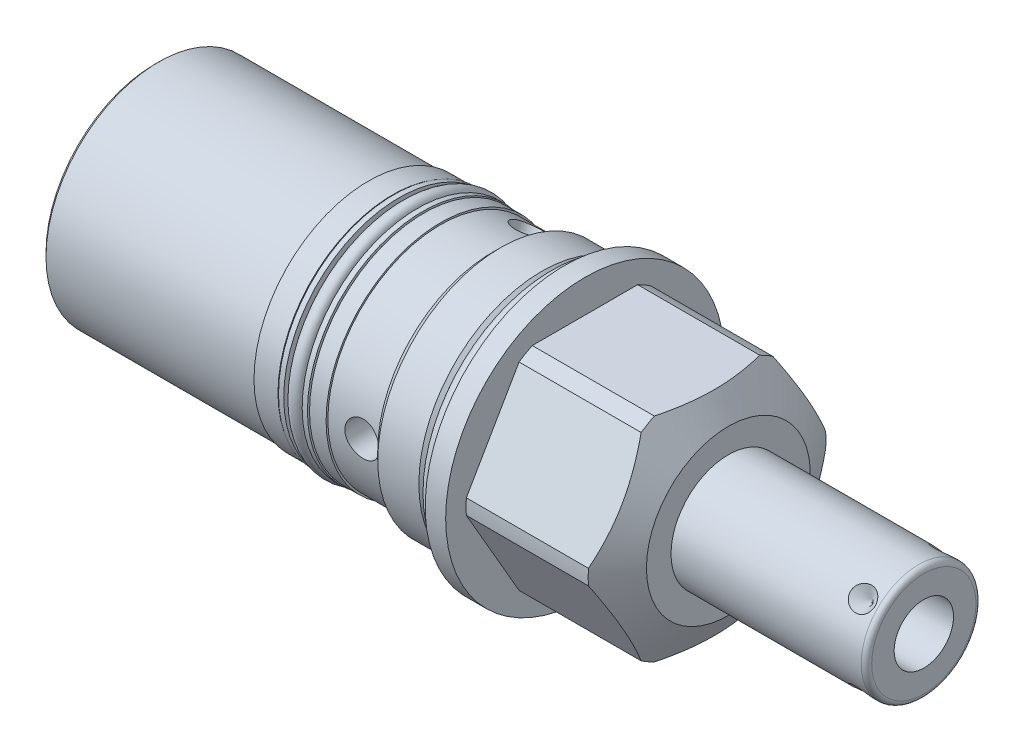
SolidWorks part; units mm, degrees
material "Alloy Steel"
ref_plane "Front Plane" through (0, 0, 0) normal (0, 0, 1) x (1, 0, 0)
ref_plane "Top Plane" through (0, 0, 0) normal (0, 1, 0) x (1, 0, 0)
ref_plane "Right Plane" through (0, 0, 0) normal (1, 0, 0) x (0, 0, -1)
ref_plane "Plane1" through (0, 0, 0) normal (1, 0, 0) x (0, 0, -1)
sketch "Sketch1" plane through (0, 0, 0) normal (1, 0, 0) x (0, 0, -1)
  circle A0 centre (0, 0) radius 26.9875
  dimension "D1" = 53.975
extrude "Extrude1" add sketch "Sketch1" along normal blind 31.75 and the other way blind 79.375
ref_plane "Plane2" through (0, 0, 0) normal (1, 0, 0) x (0, 0, -1)
sketch "Sketch2" plane through (0, 0, 0) normal (1, 0, 0) x (0, 0, -1)
  circle A0 centre (0, 0) radius 23.8125
  circle A1 centre (0, 0) radius 26.9875 construction
  circle A2 centre (0, 0) radius 26.9875
  dimension "D1" = 47.625
extrude "Cut-Extrude1" cut sketch "Sketch2" against normal up to next
ref_plane "Plane3" through (0, 0, 0) normal (0, 0, 1) x (1, 0, 0)
sketch "Sketch3" plane through (0, 0, 0) normal (0, 0, 1) x (1, 0, 0)
  line L0 (25.3342, 26.9875) -> (31.75, 15.875)
  line L1 (-8.1458, 0) -> (17.0188, 0) construction
  line L2 (31.75, 15.875) -> (31.75, 26.9875)
  line L3 (31.75, 26.9875) -> (25.3342, 26.9875)
  line L4 (31.75, 26.9875) -> (0, 26.9875) construction
  dimension "D1" = 31.75
  dimension "D2" = 30
revolve "Cut-Revolve1" cut sketch "Sketch3" angle 360 about L1
ref_plane "Plane5" through (3.175, 0, 0) normal (-1, 0, 0) x (0, 0, 1)
sketch "Sketch5" plane through (3.175, 0, 0) normal (-1, 0, 0) x (0, 0, 1)
  line L0 (-11.9151, 20.6375) -> (11.9151, 20.6375)
  line L1 (11.9151, 20.6375) -> (23.8301, 0)
  line L2 (23.8301, 0) -> (11.9151, -20.6375)
  line L3 (11.9151, -20.6375) -> (-11.9151, -20.6375)
  line L4 (-11.9151, -20.6375) -> (-23.8301, 0)
  line L5 (-23.8301, 0) -> (-11.9151, 20.6375)
  line L6 (0, 0) -> (18.7904, 0) construction
  line L7 (0, 0) -> (11.9151, 20.6375) construction
  line L8 (0, 0) -> (-11.9151, 20.6375) construction
  circle A0 centre (0, 0) radius 26.9875 construction
  circle A1 centre (0, 0) radius 26.9875
  dimension "D1" = 41.275
  dimension "D2" = 120
  dimension "D3" = 60
extrude "Cut-Extrude3" cut sketch "Sketch5" against normal up to next from offset 0.7874 offset against normal yes
ref_plane "Plane7" through (3.175, 0, 0) normal (-1, 0, 0) x (0, 0, 1)
sketch "Sketch7" plane through (3.9624, 0, 0) normal (-1, 0, 0) x (0, 0, 1)
  circle A0 centre (0, 0) radius 23.0251
  circle A1 centre (0, 0) radius 26.9875 construction
  circle A2 centre (0, 0) radius 26.9875
  dimension "D1" = 46.0502
extrude "Cut-Extrude5" cut sketch "Sketch7" against normal up to next
ref_plane "Plane9" through (0, 0, 0) normal (0, 0, 1) x (1, 0, 0)
sketch "Sketch9" plane through (0, 0, 0) normal (0, 0, 1) x (1, 0, 0)
  line L0 (0, 23.8125) -> (0, 22.3012)
  line L1 (0, 22.3012) -> (-2.8956, 22.3012)
  line L2 (-2.8956, 22.3012) -> (-4.4069, 23.8125)
  line L3 (-4.4206, 0) -> (0.2105, 0) construction
  line L4 (0, 23.8125) -> (-4.4069, 23.8125)
  line L5 (0, 23.8125) -> (-79.375, 23.8125) construction
  line L6 (0, 26.9875) -> (0, -26.9875) construction
  dimension "D1" = 2.8956
  dimension "D2" = 45
  dimension "D3" = 44.6024
revolve "Cut-Revolve3" cut sketch "Sketch9" angle 360 about L3
ref_plane "Plane10" through (0, 0, 0) normal (0, 0, 1) x (1, 0, 0)
sketch "Sketch10" plane through (0, 0, 0) normal (0, 0, 1) x (1, 0, 0)
  line L0 (-12.3698, 23.8125) -> (-13.9954, 22.1869)
  line L1 (-13.9954, 22.1869) -> (-79.375, 22.1869)
  line L2 (-55.947, 0) -> (-8.6516, 0) construction
  line L4 (-79.375, 23.8125) -> (-79.375, 22.1869)
  line L5 (-4.4069, 23.8125) -> (-4.4069, -23.8125) construction
  line L6 (-4.4069, 23.8125) -> (-79.375, 23.8125) construction
  line L7 (-12.3698, 23.8125) -> (-79.375, 23.8125)
  dimension "D1" = 44.3738
  dimension "D2" = 45
  dimension "D3" = 7.9629
revolve "Cut-Revolve4" cut sketch "Sketch10" angle 360 about L2
ref_plane "Plane12" through (0, 0, 0) normal (0, 0, 1) x (1, 0, 0)
sketch "Sketch12" plane through (0, 0, 0) normal (0, 0, 1) x (1, 0, 0)
  line L0 (-33.3248, 22.1869) -> (-33.3248, 20.1549)
  line L1 (-33.3248, 20.1549) -> (-27.2161, 20.1549)
  line L2 (-27.2161, 20.1549) -> (-27.2161, 22.1869)
  line L3 (-31.7506, 0) -> (-25.0311, 0) construction
  line L4 (-33.3248, 22.1869) -> (-27.2161, 22.1869)
  line L5 (-13.9954, 22.1869) -> (-79.375, 22.1869) construction
  line L6 (-79.375, 22.1869) -> (-79.375, -22.1869) construction
  dimension "D1" = 6.1087
  dimension "D2" = 40.3098
  dimension "D3" = 46.0502
revolve "Cut-Revolve6" cut sketch "Sketch12" angle 360 about L3
ref_plane "Plane14" through (0, 0, 0) normal (0, 0, 1) x (0, -1, 0)
sketch "Sketch14" plane through (0, 0, 0) normal (0, 0, 1) x (0, -1, 0)
  line L0 (22.1869, -79.375) -> (21.844, -79.375)
  line L1 (21.844, -79.375) -> (21.844, -37.973)
  line L2 (21.844, -37.973) -> (22.1869, -37.973)
  line L3 (22.1869, -37.973) -> (22.1869, -79.375)
  line L4 (22.1869, -13.9954) -> (21.844, -13.9954)
  line L5 (21.844, -13.9954) -> (21.844, -24.003)
  line L6 (21.844, -24.003) -> (22.1869, -24.003)
  line L7 (22.1869, -24.003) -> (22.1869, -13.9954)
  line L8 (0, -55.866) -> (0, -10.3518) construction
  line L9 (22.1869, -79.375) -> (22.1869, -33.3248) construction
  line L10 (22.1869, -27.2161) -> (22.1869, -13.9954) construction
  line L11 (-22.1869, -79.375) -> (22.1869, -79.375) construction
  dimension "D1" = 13.97
  dimension "D2" = 43.688
  dimension "D3" = 41.402
  dimension "D4" = 10.0076
revolve "Cut-Revolve8" cut sketch "Sketch14" angle 360 about L8
ref_plane "Plane15" through (0, 0, 0) normal (0, 0, 1) x (0, -1, 0)
sketch "Sketch15" plane through (0, 0, 0) normal (0, 0, 1) x (0, -1, 0)
  line L0 (0, -3.0937) -> (0, 0.1473) construction
  line L1 (-26.9875, 0) -> (26.9875, 0) construction
  circle A0 centre (23.7998, -1.4986) radius 1.4986
  dimension "D1" = 2.9972
  dimension "D2" = 1.4986
  dimension "D3" = 47.5996
revolve "Revolve1" add sketch "Sketch15" angle 360 about L0
ref_plane "Plane16" through (0, 0, 0) normal (0, 0, 1) x (0, -1, 0)
sketch "Sketch16" plane through (0, 0, 0) normal (0, 0, 1) x (0, -1, 0)
  line L0 (20.1549, -27.4701) -> (22.3393, -27.4701)
  line L1 (22.3393, -27.4701) -> (22.3393, -28.4861)
  line L2 (22.3393, -28.4861) -> (20.1549, -28.4861)
  line L3 (20.1549, -28.4861) -> (20.1549, -27.4701)
  line L4 (20.1549, -33.0708) -> (22.3393, -33.0708)
  line L5 (22.3393, -33.0708) -> (22.3393, -32.0548)
  line L6 (22.3393, -32.0548) -> (20.1549, -32.0548)
  line L7 (20.1549, -32.0548) -> (20.1549, -33.0708)
  line L8 (0, -31.4712) -> (0, -25.3105) construction
  line L9 (-22.1869, -27.2161) -> (22.1869, -27.2161) construction
  line L10 (22.1869, -33.3248) -> (-22.1869, -33.3248) construction
  line L11 (20.1549, -33.3248) -> (20.1549, -27.2161) construction
  dimension "D1" = 1.016
  dimension "D3" = 44.6786
  dimension "D4" = 0.254
  dimension "D5" = 0.254
revolve "Revolve2" add sketch "Sketch16" angle 360 about L8
ref_plane "Plane17" through (0, 0, 0) normal (0, 0, 1) x (0, -1, 0)
sketch "Sketch17" plane through (0, 0, 0) normal (0, 0, 1) x (0, -1, 0)
  line L0 (0, -31.7506) -> (0, -25.0311) construction
  line L1 (22.3393, -32.0548) -> (-22.3393, -32.0548) construction
  circle A0 centre (21.463, -30.2705) radius 1.3081
  point P0 (9.8298, -25.3365)
  point P1 (9.8298, -31.4452)
  dimension "D1" = 2.6162
  dimension "D2" = 42.926
  dimension "D3" = 1.7843
revolve "Revolve3" add sketch "Sketch17" angle 360 about L0
ref_plane "Plane18" through (0, 0, 0) normal (0, 0, 1) x (0, -1, 0)
sketch "S2D0001" plane through (0, 0, 0) normal (0, 0, 1) x (0, -1, 0)
  line L0 (0, 31.75) -> (-11.1125, 31.75)
  line L1 (-11.1125, 31.75) -> (-11.1125, 68.6054)
  line L2 (-10.0965, 69.6214) -> (0, 69.6214)
  line L3 (0, 69.6214) -> (0, 31.75)
  line L4 (0, 7.2658) -> (0, 37.3443) construction
  line L5 (15.875, 31.75) -> (-15.875, 31.75) construction
  line L6 (-26.9875, 0) -> (26.9875, 0) construction
  arc A0 (-10.0965, 69.6214) -> (-11.1125, 68.6054) centre (-10.0965, 68.6054) ccw
  dimension "D2" = 1.016
  dimension "D1" = 22.225
  dimension "D3" = 69.6214
revolve "Revolve4" add sketch "S2D0001" angle 360 about L4
ref_plane "Plane19" through (36.322, -2.8067, 0) normal (0, 0, 1) x (0, -1, 0)
sketch "Sketch19" plane through (36.322, -2.8067, 0) normal (0, 0, 1) x (0, -1, 0)
  line L0 (2.9464, 33.2994) -> (2.9464, 16.2814)
  line L1 (2.9464, 16.2814) -> (-2.8067, 12.8246)
  line L2 (2.9464, 33.2994) -> (-2.8067, 33.2994)
  line L3 (-2.8067, 33.2994) -> (-2.8067, 12.8246)
  line L4 (-2.8067, -18.6227) -> (-2.8067, 0.5923) construction
  line L5 (7.2898, 33.2994) -> (-12.9032, 33.2994) construction
  dimension "D1" = 11.5062
  dimension "D2" = 17.018
  dimension "D3" = 59
revolve "Cut-Revolve9" cut sketch "Sketch19" angle 360 about L4
ref_plane "Plane20" through (32.3596, 0, -5.5562) normal (0, 1, 0) x (1, 0, 0)
ref_plane "Plane21" through (0, 0, 0) normal (0, -0.7071, 0.7071) x (1, 0, 0)
sketch "S2D0002" plane through (32.3596, -3.9289, -3.9289) normal (0, 0.7071, -0.7071) x (1, 0, 0)
  line L0 (33.2994, 5.5563) -> (35.7124, 5.5563)
  line L1 (35.7124, 5.5563) -> (33.2994, 3.1433)
  line L2 (33.2994, 5.5563) -> (33.2994, 3.1433)
  line L3 (33.2994, -3.3652) -> (33.2994, 0.0794) construction
  line L4 (36.2458, 5.5563) -> (-0.6096, 5.5563) construction
  line L5 (37.2618, -15.6527) -> (37.2618, 4.5402) construction
  dimension "D1" = 3.9624
  dimension "D2" = 45
  dimension "D3" = 4.826
revolve "Cut-Revolve10" cut sketch "S2D0002" angle 360 about L3
chamfer "Chamfer1" distance 0.762 angle 45 1 edges at (-79.375, 0, 21.844)
sketch "Sketch23" plane through (0, 0, 0) normal (0, 0, 1) x (1, 0, 0)
  line L0 (-79.375, 21.082) -> (-79.375, -21.082) construction
  circle A0 centre (-17.399, 0) radius 3.3147
  dimension "D1" = 6.6294
  dimension "D2" = 61.976
extrude "Cut-Extrude7" cut sketch "Sketch23" along normal through all
sketch "Sketch26" plane through (-79.375, 0, 0) normal (-1, 0, 0) x (0, 0, 1)
  circle A0 centre (0, 0) radius 3.1369
  dimension "D1" = 6.2738
extrude "Cut-Extrude8" cut sketch "Sketch26" against normal blind 0.762
sketch "Sketch27" plane through (-79.375, 0, 0) normal (-1, 0, 0) x (0, 0, 1)
  circle A0 centre (0, 0) radius 17.7927
extrude "Extrude2" add sketch "Sketch27" along normal blind 0.508
sketch "Sketch28" plane through (-79.883, 0, 0) normal (-1, 0, 0) x (0, 0, 1)
  circle A0 centre (0, 0) radius 3.1369
extrude "Cut-Extrude9" cut sketch "Sketch28" against normal blind 0.508
pattern_circular "CirPattern2" count 3 over 360 about axis through (7.2658, 0, 0) along (-1, 0, 0) of "Cut-Extrude7"
pattern_circular "CirPattern3" count 4 over 360 about axis through (7.2658, 0, 0) along (-1, 0, 0) of "Cut-Revolve10"
